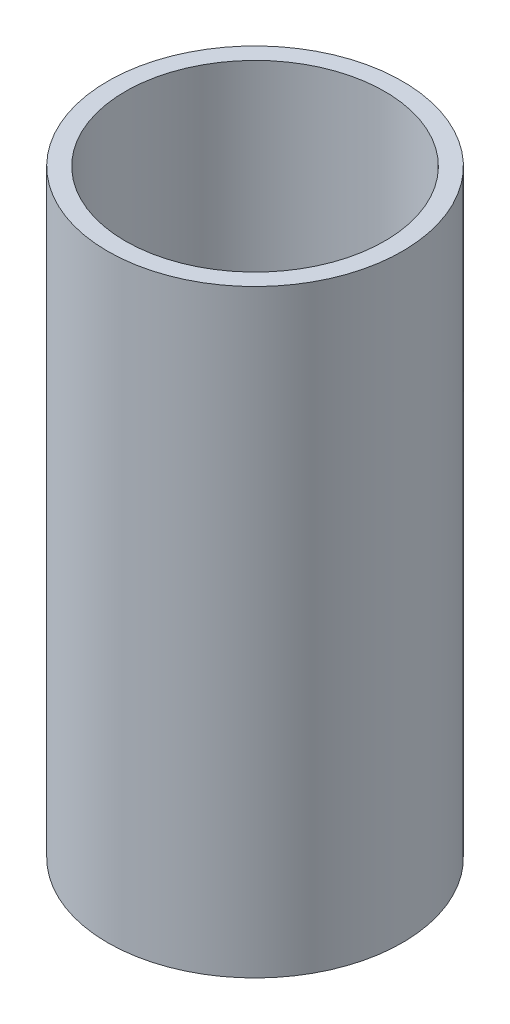
SolidWorks part; units mm, degrees
ref_plane "Front Plane" through (0, 0, 0) normal (0, 0, 1) x (1, 0, 0)
ref_plane "Top Plane" through (0, 0, 0) normal (0, 1, 0) x (1, 0, 0)
ref_plane "Right Plane" through (0, 0, 0) normal (1, 0, 0) x (0, 0, -1)
sketch "Sketch1" plane through (0, 0, 0) normal (0, 1, 0) x (1, 0, 0)
  circle A0 centre (0, 0) radius 22
  circle A1 centre (0, 0) radius 25
  dimension "D1" = 44
  dimension "D2" = 50
extrude "Boss-Extrude1" add sketch "Sketch1" along normal blind 101.6
equation "\"200.00inm\"=200"
equation "\"in200.00mm\"=200"
